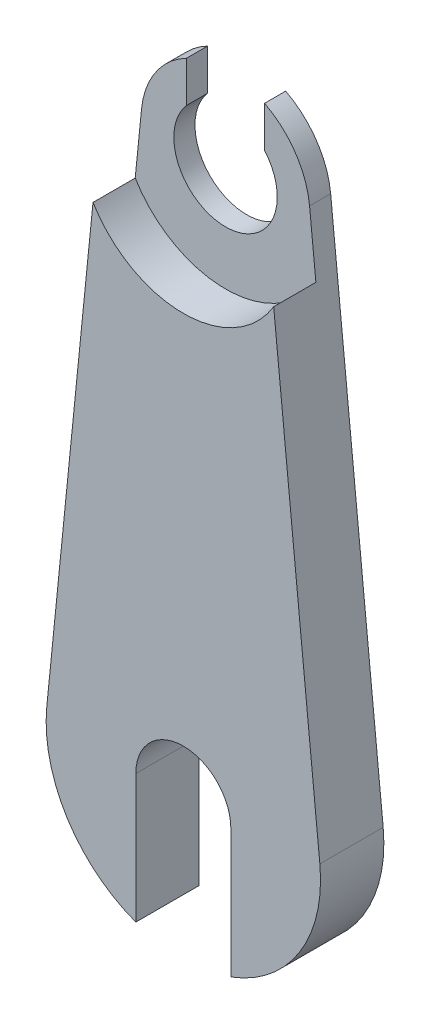
SolidWorks part; units mm, degrees
ref_plane "Front" through (0, 0, 0) normal (0, 0, 1) x (1, 0, 0)
ref_plane "Top" through (0, 0, 0) normal (0, 1, 0) x (1, 0, 0)
ref_plane "Right" through (0, 0, 0) normal (1, 0, 0) x (0, 0, -1)
sketch "Sketch3" plane through (0, 0, 0) normal (0, 0, 1) x (1, 0, 0)
  line L0 (0, 0) -> (0, -25) construction
  line L1 (3.9799, 0.4) -> (6.4674, -24.35)
  line L2 (-3.9799, 0.4) -> (-6.4674, -24.35)
  circle A0 centre (0, 0) radius 2.45
  arc A2 (3.9799, 0.4) -> (-3.9799, 0.4) centre (0, 0) ccw
  arc A3 (-6.4674, -24.35) -> (6.4674, -24.35) centre (0, -25) ccw
  point P4 (0, -10)
  point P9 (-4, -20)
  point P10 (-7.0095, -20)
  point P11 (-4, -19.6504)
  point P12 (0, 0)
  point P13 (3.9998, 1.3559)
  point P14 (6.6593, -19.0852)
  point P15 (0, 0)
  point P16 (0, 0)
  point P17 (0, 0)
  dimension "D1" = 4
  dimension "D2" = 4.9
  dimension "D4" = 6.5
  dimension "D3" = 25
extrude "Boss-Extrude1" add sketch "Sketch3" along normal blind 1
sketch "Sketch4" plane through (0, 0, 1) normal (0, 0, 1) x (1, 0, 0)
  line L1 (-1.85, 0) -> (1.85, 0)
  line L2 (-1.85, 0) -> (-1.85, 4)
  line L3 (-1.85, 4) -> (1.85, 4)
  line L4 (1.85, 0) -> (1.85, 4)
  line L5 (0, 4) -> (0, 0) construction
  line L6 (-1.85, 2) -> (1.85, 2) construction
  arc A0 (3.9799, 0.4) -> (-3.9799, 0.4) centre (0, 0) ccw construction
  point P4 (0, 0)
  point P5 (0, 4)
  point P116 (0, 2)
  dimension "D1" = 3.7
extrude "Cut-Extrude1" cut sketch "Sketch4" against normal blind 1
sketch "Sketch5" plane through (0, 0, 1) normal (0, 0, 1) x (1, 0, 0)
  line L0 (-3.9799, 0.4) -> (-6.4674, -24.35) construction
  line L1 (6.4674, -24.35) -> (3.9799, 0.4) construction
  line L4 (-1.85, 1.6062) -> (-1.85, 3.5465)
  line L5 (-3.9799, 0.4) -> (-6.4674, -24.35)
  line L6 (6.4674, -24.35) -> (3.9799, 0.4)
  line L7 (1.85, 3.5465) -> (1.85, 1.6062)
  line L9 (-4.2799, -2.585) -> (-6.4674, -24.35)
  line L10 (6.4674, -24.35) -> (4.2799, -2.585)
  arc A0 (-4.2799, -2.585) -> (4.2799, -2.585) centre (0, 0) ccw
  arc A4 (-1.85, 3.5465) -> (-3.9799, 0.4) centre (0, 0) ccw
  arc A5 (-6.4674, -24.35) -> (6.4674, -24.35) centre (0, -25) ccw
  arc A6 (3.9799, 0.4) -> (1.85, 3.5465) centre (0, 0) ccw
  arc A7 (-1.85, 1.6062) -> (1.85, 1.6062) centre (0, 0) ccw
  arc A9 (-6.4674, -24.35) -> (6.4674, -24.35) centre (0, -25) ccw
  point P2 (0, 0)
  point P7 (-3.9686, 0.5)
  point P11 (-4.299, -2.1222)
  point P19 (4.3364, -2.4188)
  point P23 (0, 0)
  point P25 (-4.1945, -1.2927)
  dimension "D2" = 5
  dimension "D1" = 0
extrude "Boss-Extrude2" add sketch "Sketch5" along normal blind 2
sketch "Sketch6" plane through (0, 0, 3) normal (0, 0, 1) x (1, 0, 0)
  line L0 (0, -25) -> (0, -31.5) construction
  line L1 (2.25, -25) -> (2.25, -31.5)
  line L2 (-2.25, -25) -> (-2.25, -31.5)
  arc A0 (2.25, -25) -> (-2.25, -25) centre (0, -25) ccw
  arc A1 (-2.25, -31.5) -> (2.25, -31.5) centre (0, -31.5) ccw
  arc A2 (-6.4674, -24.35) -> (6.4674, -24.35) centre (0, -25) ccw construction
  point P4 (0, -28.25)
  point P9 (0, -31.5)
  dimension "D1" = 4.5
extrude "Cut-Extrude2" cut sketch "Sketch6" against normal through all
